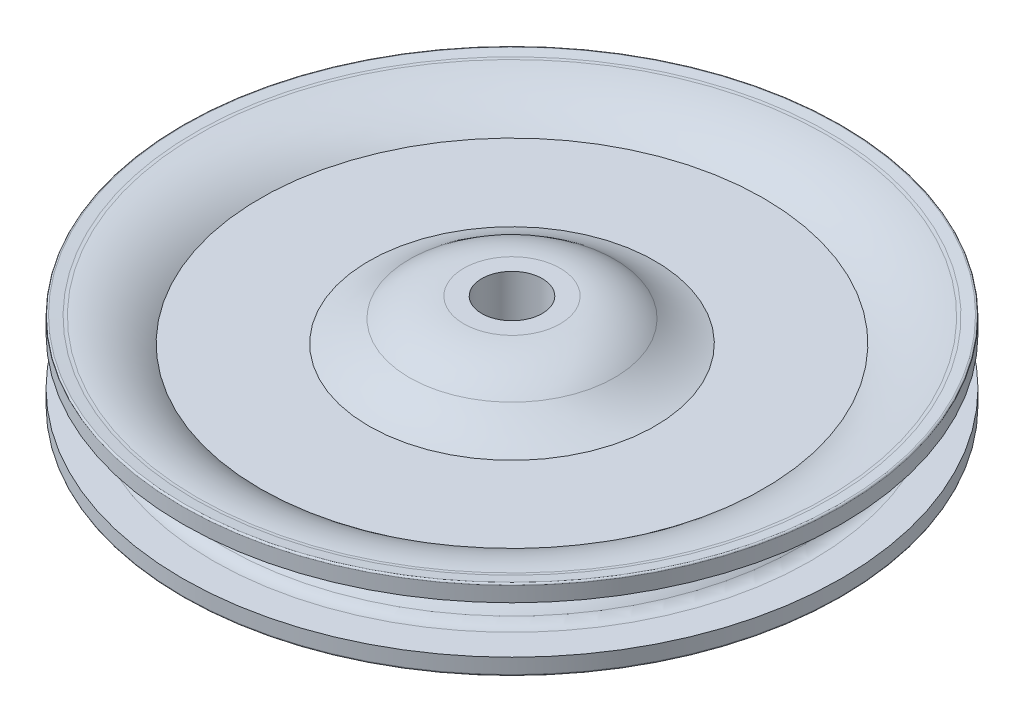
SolidWorks part; units mm, degrees
ref_plane "Front Plane" through (0, 0, 0) normal (0, 0, 1) x (1, 0, 0)
ref_plane "Top Plane" through (0, 0, 0) normal (0, 1, 0) x (1, 0, 0)
ref_plane "Right Plane" through (0, 0, 0) normal (1, 0, 0) x (0, 0, -1)
sketch "Sketch1" plane through (0, 0, 0) normal (0, 0, 1) x (1, 0, 0)
  line L0 (-29.7561, 0) -> (52.1913, 0) construction
  line L1 (0, 28.5753) -> (0, -17.712) construction
  line L2 (4.9594, -9.2139) -> (4.9594, 9.2139)
  line L3 (4.9594, 9.2139) -> (7.8931, 9.2138)
  line L4 (4.9594, -9.2139) -> (7.8931, -9.2138)
  line L7 (23.4315, 2.4765) -> (41.2115, 2.4765)
  line L8 (23.4315, -2.4765) -> (41.2115, -2.4765)
  line L13 (51.9935, 6.3803) -> (53.6796, 6.5719)
  line L14 (51.7271, -6.35) -> (53.6796, -6.5719)
  line L17 (53.9623, 6.3195) -> (53.9623, 3.8608)
  line L18 (53.9623, 3.8608) -> (48.9657, 3.8608)
  line L20 (48.9657, -3.8608) -> (53.9623, -3.8608)
  line L21 (53.9623, -3.8608) -> (53.9623, -6.3195)
  arc A0 (51.4932, 6.3483) -> (41.2115, 2.4765) centre (51.7271, -9.8604) ccw
  arc A1 (51.7271, -6.35) -> (41.2115, -2.4765) centre (51.7271, 9.8604) cw
  arc A2 (7.8931, 9.2138) -> (16.8021, 6.0352) centre (7.8931, -4.8604) cw
  arc A3 (7.8931, -9.2138) -> (16.8021, -6.0352) centre (7.8931, 4.8604) ccw
  arc A4 (16.8021, 6.0352) -> (23.4315, 2.4765) centre (29.2324, 21.2372) ccw
  arc A5 (16.8021, -6.0352) -> (23.4315, -2.4765) centre (29.2324, -21.2372) cw
  arc A6 (53.6796, 6.5719) -> (53.9623, 6.3195) centre (53.7083, 6.3195) cw
  arc A7 (53.9623, -6.3195) -> (53.6796, -6.5719) centre (53.7083, -6.3195) cw
  arc A8 (51.4932, 6.3483) -> (51.9935, 6.3803) centre (51.4199, 11.4278) ccw
  arc A9 (47.0103, 2.9419) -> (43.6, 0) centre (36.5684, 11.5987) cw
  arc A10 (47.0103, -2.9419) -> (43.6, 0) centre (36.5684, -11.5987) ccw
  arc A11 (48.9657, 3.8608) -> (47.0103, 2.9419) centre (48.9657, 1.3208) ccw
  arc A12 (47.0103, -2.9419) -> (48.9657, -3.8608) centre (48.9657, -1.3208) ccw
  point P8 (4.9594, 0)
  point P20 (53.9623, 0)
  point P21 (53.9623, 0)
  point P37 (53.9623, 6.604)
  point P40 (53.9623, -6.604)
  point P41 (51.7271, 6.35)
  point P46 (47.7083, 3.8608)
  point P49 (47.7083, -3.8608)
  dimension "D13" = 0.254
  dimension "D14" = 0.254
  dimension "D5" = 5.08
  dimension "D16" = 2.54
  dimension "D17" = 2.54
  dimension "D1" = 4.9594
  dimension "D2" = 7.8931
  dimension "D3" = 23.4315
  dimension "D4" = 41.2115
  dimension "D6" = 53.9623
  dimension "D7" = 2.2352
  dimension "D8" = 7.7216
  dimension "D9" = 13.208
  dimension "D10" = 0.254
  dimension "D11" = 4.953
  dimension "D12" = 18.4277
  dimension "D15" = 16.8021
revolve "Revolve1" add sketch "Sketch1" angle 360 about L1
